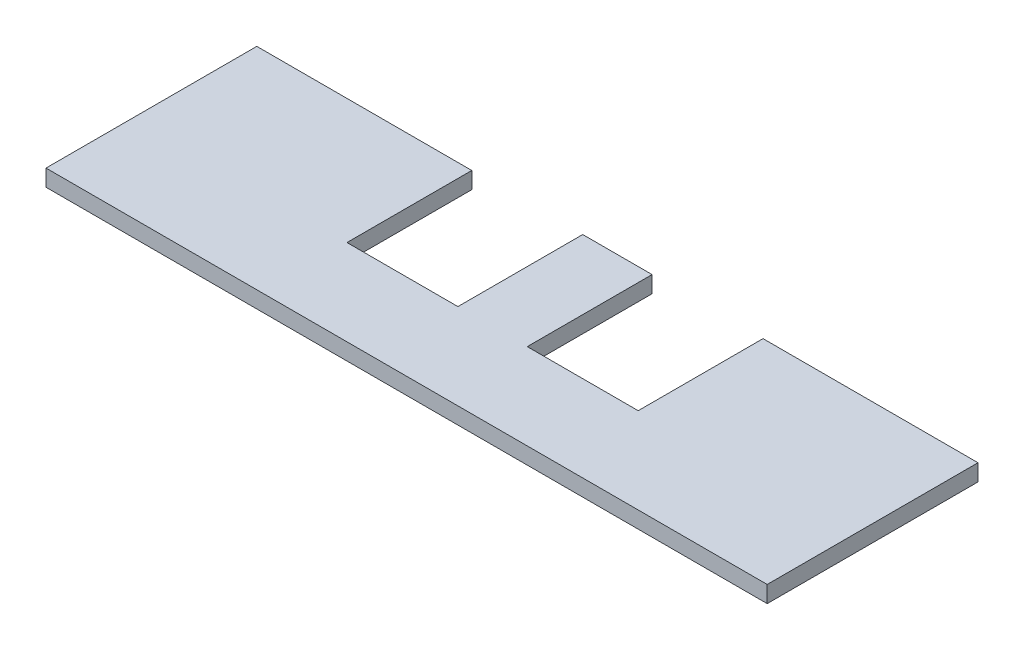
SolidWorks part; units mm, degrees
ref_plane "Front Plane" through (0, 0, 0) normal (0, 0, 1) x (1, 0, 0)
ref_plane "Top Plane" through (0, 0, 0) normal (0, 1, 0) x (1, 0, 0)
ref_plane "Right Plane" through (0, 0, 0) normal (1, 0, 0) x (0, 0, -1)
sketch "Sketch1" plane through (0, 0, 0) normal (0, 1, 0) x (1, 0, 0)
  line L1 (-65, -60) -> (65, -60)
  line L2 (-65, -60) -> (-65, 60)
  line L3 (-65, 60) -> (65, 60)
  line L4 (65, -60) -> (65, 60)
  line L5 (-65, -60) -> (65, 60) construction
  line L6 (-65, 60) -> (65, -60) construction
  point P0 (0, 0)
  dimension "D1" = 130
  dimension "D2" = 120
extrude "Boss-Extrude1" add sketch "Sketch1" along normal blind 3
sketch "Sketch2" plane through (0, 3, 0) normal (0, 1, 0) x (1, 0, 0)
  line L1 (-26.25, -44.5) -> (-6.25, -44.5)
  line L2 (-26.25, -44.5) -> (-26.25, 44.5)
  line L3 (-26.25, 44.5) -> (-6.25, 44.5)
  line L4 (-6.25, -44.5) -> (-6.25, 44.5)
  line L5 (-26.25, -44.5) -> (-6.25, 44.5) construction
  line L6 (-26.25, 44.5) -> (-6.25, -44.5) construction
  point P0 (-16.25, 0)
  dimension "D1" = 89
  dimension "D2" = 20
  dimension "D3" = 6.25
extrude "Cut-Extrude1" cut sketch "Sketch2" against normal through all both and the other way through all
mirror "Mirror1" about plane through (0, 0, 0) normal (1, 0, 0) of "Cut-Extrude1"
sketch "Sketch3" plane through (0, 3, 0) normal (0, 1, 0) x (1, 0, 0)
  circle A0 centre (44.5, 0) radius 1.6
  dimension "D1" = 3.2
  dimension "D2" = 44.5
extrude "Cut-Extrude2" cut sketch "Sketch3" against normal through all both and the other way through all
mirror "Mirror2" about plane through (0, 0, 0) normal (1, 0, 0) of "Cut-Extrude2"
sketch "Sketch4" plane through (0, 3, 0) normal (0, 1, 0) x (1, 0, 0)
  line L0 (-65, 60) -> (-65, -60) construction
  line L1 (-65, -22) -> (65, -22)
  line L2 (-65, -22) -> (-65, 60)
  line L3 (-65, 60) -> (65, 60)
  line L4 (65, -22) -> (65, 60)
  circle A0 centre (-44.5, 0) radius 1.6 construction
  dimension "D1" = 22
extrude "Cut-Extrude3" cut sketch "Sketch4" against normal through all both and the other way through all
